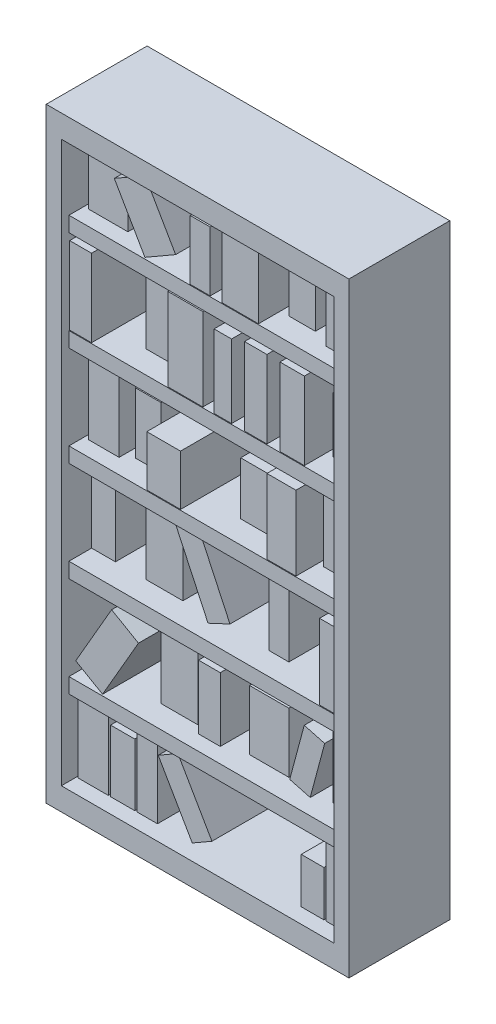
SolidWorks part; units mm, degrees
ref_plane "Front Plane" through (0, 0, 0) normal (0, 0, 1) x (1, 0, 0)
ref_plane "Top Plane" through (0, 0, 0) normal (0, 1, 0) x (1, 0, 0)
ref_plane "Right Plane" through (0, 0, 0) normal (1, 0, 0) x (0, 0, -1)
sketch "Sketch1" plane through (0, 0, 0) normal (0, 1, 0) x (1, 0, 0)
  line L1 (-50, 16.6667) -> (50, 16.6667)
  line L2 (-50, 16.6667) -> (-50, -16.6667)
  line L3 (-50, -16.6667) -> (50, -16.6667)
  line L4 (50, 16.6667) -> (50, -16.6667)
  line L5 (-50, 16.6667) -> (50, -16.6667) construction
  line L6 (-50, -16.6667) -> (50, 16.6667) construction
  point P0 (0, 0)
  dimension "D1" = 100
  dimension "D2" = 33.3333
extrude "Boss-Extrude1" add sketch "Sketch1" along normal mid plane 200
sketch "Sketch2" plane through (0, 0, 16.6667) normal (0, 0, 1) x (1, 0, 0)
  line L0 (50, 100) -> (50, -100) construction
  line L1 (-45, 92.5) -> (45, 92.5)
  line L2 (-45, 92.5) -> (-45, -92.5)
  line L3 (-45, -92.5) -> (45, -92.5)
  line L4 (45, 92.5) -> (45, -92.5)
  line L5 (-45, 92.5) -> (45, -92.5) construction
  line L6 (-45, -92.5) -> (45, 92.5) construction
  line L7 (-50, -100) -> (50, -100) construction
  point P0 (0, 0)
  dimension "D1" = 5
  dimension "D2" = 7.5
extrude "Cut-Extrude1" cut sketch "Sketch2" against normal blind 27.5
sketch "Sketch3" plane through (0, 0, -10.8333) normal (0, 0, 1) x (1, 0, 0)
  line L0 (45, -92.5) -> (45, 92.5) construction
  line L1 (45, -62.5) -> (-45, -62.5)
  line L2 (45, -62.5) -> (45, -67.5)
  line L3 (45, -67.5) -> (-45, -67.5)
  line L4 (-45, -62.5) -> (-45, -67.5)
  line L5 (-45, 92.5) -> (-45, -92.5) construction
  line L6 (-45, -92.5) -> (45, -92.5) construction
  line L7 (45, -29.5) -> (-45, -29.5)
  line L8 (45, -34.5) -> (-45, -34.5)
  line L9 (45, -29.5) -> (45, -34.5)
  line L10 (-45, -29.5) -> (-45, -34.5)
  line L11 (45, 3.5) -> (-45, 3.5)
  line L12 (45, -1.5) -> (-45, -1.5)
  line L13 (45, 3.5) -> (45, -1.5)
  line L14 (-45, 3.5) -> (-45, -1.5)
  line L15 (45, 36.5) -> (-45, 36.5)
  line L16 (45, 31.5) -> (-45, 31.5)
  line L17 (45, 36.5) -> (45, 31.5)
  line L18 (-45, 36.5) -> (-45, 31.5)
  line L19 (45, 69.5) -> (-45, 69.5)
  line L20 (45, 64.5) -> (-45, 64.5)
  line L21 (45, 69.5) -> (45, 64.5)
  line L22 (-45, 69.5) -> (-45, 64.5)
  dimension "D1" = 25
  dimension "D2" = 5
  dimension "D4" = 33
  dimension "D3" = 5
extrude "Boss-Extrude2" add sketch "Sketch3" along normal blind 25
sketch "Sketch4" plane through (0, 0, -10.8333) normal (0, 0, 1) x (1, 0, 0)
  line L0 (37.5, -92.5) -> (37.5, -70)
  line L1 (-45, -92.5) -> (45, -92.5) construction
  line L2 (37.5, -70) -> (45, -70)
  line L3 (45, -92.5) -> (45, 92.5) construction
  line L4 (45, -70) -> (45, -92.5)
  line L5 (45, -92.5) -> (37.5, -92.5)
  line L6 (36.75, -92.5) -> (36.75, -77.5)
  line L7 (-45, -92.5) -> (45, -92.5) construction
  line L8 (36.75, -77.5) -> (29.25, -77.5)
  line L9 (29.25, -77.5) -> (29.25, -92.5)
  line L10 (29.25, -92.5) -> (36.75, -92.5)
  line L11 (-44.5, -92.5) -> (-44.5, -70)
  line L12 (-44.5, -70) -> (-34.5, -70)
  line L13 (-34.5, -70) -> (-34.5, -92.5)
  line L14 (-34.5, -92.5) -> (-44.5, -92.5)
  line L15 (-45, 92.5) -> (-45, -92.5) construction
  line L16 (-33.7477, -92.5) -> (-33.7477, -72)
  line L17 (-33.7477, -72) -> (-25.7477, -72)
  line L18 (-25.7477, -72) -> (-25.7477, -92.5)
  line L19 (-25.7477, -92.5) -> (-33.7477, -92.5)
  line L20 (-24.9977, -92.5) -> (-24.9977, -70)
  line L21 (-24.9977, -70) -> (-18.2477, -70)
  line L22 (-18.2477, -70) -> (-18.2477, -92.5)
  line L23 (-18.2477, -92.5) -> (-24.9977, -92.5)
  line L24 (-17.9977, -72.7644) -> (-6.7477, -92.25)
  line L25 (-6.7477, -92.25) -> (-0.2525, -88.5)
  line L26 (-0.2525, -88.5) -> (-11.5025, -69.0144)
  line L27 (-11.5025, -69.0144) -> (-17.9977, -72.7644)
  line L28 (-17.9977, -70) -> (-17.9977, -92.5) construction
  line L29 (-18.2477, -92.25) -> (29.25, -92.25) construction
  point P25 (-29.7477, -72)
  point P34 (0, 0)
  dimension "D1" = 22.5
  dimension "D2" = 7.5
  dimension "D3" = 7.5
  dimension "D4" = 15
  dimension "D5" = 0.75
  dimension "D6" = 10
  dimension "D7" = 0.5
  dimension "D8" = 0.7523
  dimension "D9" = 2
  dimension "D10" = 8
  dimension "D11" = 0.75
  dimension "D12" = 7.5
  dimension "D13" = 30
  dimension "D14" = 7.5
  dimension "D15" = 22.5
  dimension "D16" = 0.25
  dimension "D17" = 0.25
extrude "Boss-Extrude5" add sketch "Sketch4" along normal offset from surface (22.5 mm away) 5 contours L14 L11 L12 L13 | L19 L16 L17 L18 | L23 L20 L21 L22 | L27 L24 L25 L26 | L10 L6 L8 L9 | L5 L0 L2 L4 up to face at (0, 0, 16.6667)
sketch "Sketch5" plane through (0, 0, -10.8333) normal (0, 0, 1) x (1, 0, 0)
  line L0 (45, -62.5) -> (45, -40.0606)
  line L1 (45, -92.5) -> (45, 92.5) construction
  line L2 (45, -40.0606) -> (34.7546, -40.0606)
  line L3 (34.7546, -40.0606) -> (34.7546, -62.5)
  line L4 (45, -62.5) -> (-45, -62.5) construction
  line L5 (34.7546, -62.5) -> (45, -62.5)
  line L6 (20.163, -42.7136) -> (7.1632, -42.7136)
  line L7 (7.1632, -42.7136) -> (7.1632, -62.5)
  line L8 (7.1632, -62.5) -> (20.163, -62.5)
  line L9 (45, -62.5) -> (-45, -62.5) construction
  line L10 (20.163, -62.5) -> (20.163, -42.7136)
  line L11 (-9.8162, -62.5) -> (-9.8162, -36.877)
  line L12 (-9.8162, -36.877) -> (-22.0201, -36.877)
  line L13 (-22.0201, -36.877) -> (-22.0201, -62.5)
  line L14 (-22.0201, -62.5) -> (-9.8162, -62.5)
  line L15 (-45, -6.3672) -> (-37.1423, -6.3672)
  line L16 (-45, -1.5) -> (-45, -29.5) construction
  line L17 (-37.1423, -6.3672) -> (-37.1423, -29.5)
  line L18 (45, -29.5) -> (-45, -29.5) construction
  line L19 (-37.1423, -29.5) -> (-45, -29.5)
  line L20 (-45, -29.5) -> (-45, -6.3672)
  line L21 (-27.0608, -4.5) -> (-14.8569, -4.5)
  line L22 (-14.8569, -4.5) -> (-14.8569, -29.5)
  line L23 (45, -29.5) -> (-45, -29.5) construction
  line L24 (-14.8569, -29.5) -> (-27.0608, -29.5)
  line L25 (-27.0608, -29.5) -> (-27.0608, -4.5)
  line L26 (13.5304, -29.5) -> (13.5304, -8.755)
  line L27 (13.5304, -8.755) -> (20.163, -8.755)
  line L28 (20.163, -8.755) -> (20.163, -29.5)
  line L29 (20.163, -29.5) -> (13.5304, -29.5)
  line L30 (42, 3.5) -> (42, 25.9996)
  line L31 (45, 3.5) -> (-45, 3.5) construction
  line L32 (42, 25.9996) -> (31.6532, 25.9996)
  line L33 (31.6532, 25.9996) -> (31.6532, 3.5)
  line L34 (31.6532, 3.5) -> (42, 3.5)
  line L35 (16.8467, 3.5) -> (16.8467, 20.9589)
  line L36 (45, 3.5) -> (-45, 3.5) construction
  line L37 (16.8467, 20.9589) -> (4.2448, 20.9589)
  line L38 (4.2448, 20.9589) -> (4.2448, 3.5)
  line L39 (4.2448, 3.5) -> (16.8467, 3.5)
  line L40 (-22.0201, 3.5) -> (-22.0201, 23.6119)
  line L41 (-22.0201, 23.6119) -> (-30.5097, 23.6119)
  line L42 (-30.5097, 23.6119) -> (-30.5097, 3.5)
  line L43 (-30.5097, 3.5) -> (-22.0201, 3.5)
  line L44 (45, 54.9175) -> (34.7546, 54.9175)
  line L45 (45, 36.5) -> (45, 64.5) construction
  line L46 (34.7546, 54.9175) -> (34.7546, 36.5)
  line L47 (45, 36.5) -> (-45, 36.5) construction
  line L48 (34.7546, 36.5) -> (45, 36.5)
  line L49 (45, 36.5) -> (-45, 36.5) construction
  line L50 (45, 36.5) -> (45, 54.9175)
  line L51 (-14.8569, 36.5) -> (-14.8569, 58.3664)
  line L52 (-14.8569, 58.3664) -> (-27.0608, 58.3664)
  line L53 (-27.0608, 58.3664) -> (-27.0608, 36.5)
  line L54 (-27.0608, 36.5) -> (-14.8569, 36.5)
  line L55 (20.163, 69.5) -> (20.163, 89.1415)
  line L56 (45, 69.5) -> (-45, 69.5) construction
  line L57 (20.163, 89.1415) -> (28.9179, 89.1415)
  line L58 (28.9179, 89.1415) -> (28.9179, 69.5)
  line L59 (45, 69.5) -> (-45, 69.5) construction
  line L60 (28.9179, 69.5) -> (20.163, 69.5)
  line L61 (-45, 92.5) -> (-45, -92.5) construction
  dimension "D1" = 22.4394
  dimension "D2" = 10.2454
  dimension "D3" = 12.9998
  dimension "D4" = 19.7864
  dimension "D5" = 14.5916
  dimension "D6" = 16.9793
  dimension "D7" = 25.623
  dimension "D8" = 12.2039
  dimension "D9" = 20.745
  dimension "D10" = 6.6326
  dimension "D11" = 12.2039
  dimension "D12" = 23.1328
  dimension "D13" = 7.8577
  dimension "D14" = 10.0815
  dimension "D15" = 25
  dimension "D16" = 8.4897
  dimension "D17" = 20.1119
  dimension "D18" = 12.6018
  dimension "D19" = 17.4589
  dimension "D20" = 26.2649
  dimension "D21" = 10.3468
  dimension "D22" = 22.4996
  dimension "D23" = 3
  dimension "D24" = 18.4175
  dimension "D25" = 10.2454
  dimension "D26" = 21.8664
  dimension "D27" = 17.9392
  dimension "D28" = 8.755
  dimension "D29" = 19.6415
extrude "Boss-Extrude6" add sketch "Sketch5" along normal offset from surface (17.5 mm away) 10 contours L60 L55 L57 L58 | L54 L51 L52 L53 | L50 L44 L46 L48 | L39 L35 L37 L38 | L34 L30 L32 L33 | L43 L40 L41 L42 | L25 L21 L22 L24 | L20 L15 L17 L19 | L29 L26 L27 L28 | L14 L11 L12 L13 | L10 L6 L7 L8 | L5 L0 L2 L3 up to face at (0, 0, 16.6667)
sketch "Sketch6" plane through (0, 0, -10.8333) normal (0, 0, 1) x (1, 0, 0)
  line L0 (-7.1632, -62.5) -> (-7.1632, -41.3871)
  line L1 (45, -62.5) -> (-45, -62.5) construction
  line L2 (-7.1632, -41.3871) -> (0, -41.3871)
  line L3 (0, -41.3871) -> (0, -62.5)
  line L4 (0, -62.5) -> (-7.1632, -62.5)
  line L5 (27.7431, -42.5686) -> (34.5046, -44.3804)
  line L6 (34.5046, -44.3804) -> (29.7164, -62.25)
  line L7 (29.7164, -62.25) -> (22.9549, -60.4383)
  line L8 (22.9549, -60.4383) -> (27.7431, -42.5686)
  line L9 (-14.6069, -6.5923) -> (-4.0415, -29.25)
  line L10 (-4.0415, -29.25) -> (3.209, -25.8691)
  line L11 (3.209, -25.8691) -> (-7.3565, -3.2114)
  line L12 (-7.3565, -3.2114) -> (-14.6069, -6.5923)
  line L13 (-43.5, 28.4287) -> (-33.4282, 28.4287)
  line L14 (-33.4282, 28.4287) -> (-33.4282, 3.5)
  line L15 (-30.5097, 3.5) -> (-45, 3.5) construction
  line L16 (-33.4282, 3.5) -> (-43.5, 3.5)
  line L17 (-43.5, 3.5) -> (-43.5, 28.4287)
  line L18 (34.8604, 92.5) -> (34.8604, 69.5)
  line L19 (45, 92.5) -> (-45, 92.5) construction
  line L20 (45, 69.5) -> (28.9179, 69.5) construction
  line L21 (34.8604, 69.5) -> (42.5, 69.5)
  line L22 (45, 69.5) -> (-45, 69.5) construction
  line L23 (42.5, 69.5) -> (42.5, 92.5)
  line L24 (42.5, 92.5) -> (34.8604, 92.5)
  line L25 (-43.5, 69.5) -> (-43.5, 89.2312)
  line L26 (20.163, 69.5) -> (-45, 69.5) construction
  line L27 (-43.5, 89.2312) -> (-30.5097, 89.2312)
  line L28 (-30.5097, 89.2312) -> (-30.5097, 69.5)
  line L29 (-30.5097, 69.5) -> (-43.5, 69.5)
  line L30 (34.5046, -40.0606) -> (34.5046, -62.5) construction
  line L31 (45, -40.0606) -> (34.7546, -40.0606) construction
  line L32 (34.7546, -62.5) -> (34.7546, -40.0606) construction
  line L33 (34.5046, -62.25) -> (20.163, -62.25) construction
  line L34 (20.163, -42.7136) -> (20.163, -62.5) construction
  line L35 (34.7546, -62.5) -> (20.163, -62.5) construction
  line L36 (-14.6069, -29.5) -> (-14.6069, -4.5) construction
  line L37 (13.5304, -29.5) -> (-14.8569, -29.5) construction
  line L38 (-27.0608, -4.5) -> (-14.8569, -4.5) construction
  line L39 (-14.8569, -29.5) -> (-14.8569, -4.5) construction
  line L40 (-14.8569, -29.25) -> (13.5304, -29.25) construction
  line L41 (13.5304, -8.755) -> (13.5304, -29.5) construction
  line L42 (-45, 92.5) -> (-45, -92.5) construction
  line L43 (45, 69.5) -> (45, 92.5) construction
  point P52 (0, 0)
  dimension "D1" = 7.1632
  dimension "D2" = 21.1129
  dimension "D3" = 0.25
  dimension "D4" = 0.25
  dimension "D5" = 15
  dimension "D6" = 7
  dimension "D7" = 18.5
  dimension "D8" = 0.25
  dimension "D9" = 0.25
  dimension "D10" = 25
  dimension "D11" = 8
  dimension "D12" = 25
  dimension "D13" = 24.9287
  dimension "D14" = 1.5
  dimension "D15" = 10.0718
  dimension "D16" = 12.9903
  dimension "D17" = 19.7312
  dimension "D18" = 7.6396
  dimension "D19" = 2.5
extrude "Boss-Extrude7" add sketch "Sketch6" along normal offset from surface (20 mm away) 7.5 up to face at (0, 0, 16.6667)
sketch "Sketch7" plane through (0, 0, -10.8333) normal (0, 0, 1) x (1, 0, 0)
  line L0 (-22.2701, -41.7032) -> (-31.1443, -36.5797)
  line L1 (-31.1443, -36.5797) -> (-43.007, -57.1265)
  line L2 (-43.007, -57.1265) -> (-34.1328, -62.25)
  line L3 (-34.1328, -62.25) -> (-22.2701, -41.7032)
  line L4 (37.5569, -29.5) -> (37.5569, -4.6754)
  line L5 (45, -29.5) -> (-45, -29.5) construction
  line L6 (37.5569, -4.6754) -> (45, -4.6754)
  line L7 (45, -29.5) -> (45, -1.5) construction
  line L8 (45, -4.6754) -> (45, -29.5)
  line L9 (45, -29.5) -> (20.163, -29.5) construction
  line L10 (45, -29.5) -> (37.5569, -29.5)
  line L11 (-19.5201, 3.5) -> (-19.5201, 20.1913)
  line L12 (4.2448, 3.5) -> (-22.0201, 3.5) construction
  line L13 (-19.5201, 20.1913) -> (-8.3782, 20.1913)
  line L14 (-8.3782, 20.1913) -> (-8.3782, 3.5)
  line L15 (-8.3782, 3.5) -> (-19.5201, 3.5)
  line L16 (29.7606, 28.0763) -> (29.7606, 3.5)
  line L17 (31.6532, 3.5) -> (16.8467, 3.5) construction
  line L18 (29.7606, 3.5) -> (20.163, 3.5)
  line L19 (20.163, 3.5) -> (20.163, 28.0763)
  line L20 (20.163, 28.0763) -> (29.7606, 28.0763)
  line L21 (-45, 62.1169) -> (-37.7779, 62.1169)
  line L22 (-45, 64.5) -> (-45, 36.5) construction
  line L23 (-37.7779, 62.1169) -> (-37.7779, 36.5)
  line L24 (-27.0608, 36.5) -> (-45, 36.5) construction
  line L25 (-37.7779, 36.5) -> (-45, 36.5)
  line L26 (-45, 36.5) -> (-45, 62.1169)
  line L27 (-12.5725, 36.5) -> (-12.5725, 63.8038)
  line L28 (34.7546, 36.5) -> (-14.8569, 36.5) construction
  line L29 (-12.5725, 63.8038) -> (-1.0052, 63.8038)
  line L30 (-1.0052, 63.8038) -> (-1.0052, 36.5)
  line L31 (-1.0052, 36.5) -> (-12.5725, 36.5)
  line L32 (2.7125, 36.5) -> (2.7125, 60.6988)
  line L33 (45, 36.5) -> (-45, 36.5) construction
  line L34 (2.7125, 60.6988) -> (8.4868, 60.6988)
  line L35 (8.4868, 60.6988) -> (8.4868, 36.5)
  line L36 (8.4868, 36.5) -> (2.7125, 36.5)
  line L37 (12.7582, 62.1169) -> (20.163, 62.1169)
  line L38 (20.163, 62.1169) -> (20.163, 36.5)
  line L39 (20.163, 36.5) -> (12.7582, 36.5)
  line L40 (12.7582, 36.5) -> (12.7582, 62.1169)
  line L41 (24.4649, 62.1169) -> (24.4649, 36.5)
  line L42 (24.4649, 36.5) -> (32.533, 36.5)
  line L43 (32.533, 36.5) -> (32.533, 62.1169)
  line L44 (32.533, 62.1169) -> (24.4649, 62.1169)
  line L45 (-30.2597, 87.2849) -> (-20.1359, 69.75)
  line L46 (45, 69.5) -> (-45, 69.5) construction
  line L47 (-20.1359, 69.75) -> (-9.9949, 75.605)
  line L48 (-9.9949, 75.605) -> (-20.1187, 93.1399)
  line L49 (-20.1187, 93.1399) -> (-30.2597, 87.2849)
  line L50 (17.3755, 69.5) -> (17.3755, 91.527)
  line L51 (20.163, 69.5) -> (-30.5097, 69.5) construction
  line L52 (17.3755, 91.527) -> (5.3398, 91.527)
  line L53 (5.3398, 91.527) -> (5.3398, 69.5)
  line L54 (5.3398, 69.5) -> (17.3755, 69.5)
  line L55 (1.4321, 69.5) -> (1.4321, 89.2129)
  line L56 (1.4321, 89.2129) -> (-5.1734, 89.2129)
  line L57 (-5.1734, 89.2129) -> (-5.1734, 69.5)
  line L58 (-5.1734, 69.5) -> (1.4321, 69.5)
  line L59 (-22.2701, -62.5) -> (-22.2701, -36.877) construction
  line L60 (-22.0201, -62.5) -> (-45, -62.5) construction
  line L61 (-9.8162, -36.877) -> (-22.0201, -36.877) construction
  line L62 (-22.0201, -62.5) -> (-22.0201, -36.877) construction
  line L63 (-22.0201, -62.25) -> (-45, -62.25) construction
  line L64 (-45, 92.5) -> (-45, -92.5) construction
  line L65 (45, -62.5) -> (-45, -62.5) construction
  line L66 (31.6532, 3.5) -> (31.6532, 25.9996) construction
  line L67 (-22.0201, 3.5) -> (-22.0201, 23.6119) construction
  line L68 (34.7546, 54.9175) -> (34.7546, 36.5) construction
  line L69 (20.163, 69.5) -> (20.163, 89.1415) construction
  line L70 (-30.2597, 69.5) -> (-30.2597, 89.2312) construction
  line L71 (-30.5097, 89.2312) -> (-43.5, 89.2312) construction
  line L72 (-30.5097, 89.2312) -> (-30.5097, 69.5) construction
  line L73 (-30.2597, 69.75) -> (-5.1734, 69.75) construction
  point P85 (0, 0)
  point P100 (0, 0)
  dimension "D1" = 0.25
  dimension "D2" = 0.25
  dimension "D3" = 10.247
  dimension "D4" = 23.7254
  dimension "D5" = 30
  dimension "D6" = 7.4431
  dimension "D7" = 24.8246
  dimension "D8" = 9.5976
  dimension "D9" = 1.8926
  dimension "D10" = 24.5763
  dimension "D11" = 16.6913
  dimension "D12" = 11.1419
  dimension "D13" = 2.5
  dimension "D14" = 7.2221
  dimension "D15" = 25.6169
  dimension "D16" = 8.0682
  dimension "D17" = 25.6169
  dimension "D18" = 2.2215
  dimension "D19" = 7.4048
  dimension "D20" = 4.2714
  dimension "D21" = 24.1988
  dimension "D22" = 5.7743
  dimension "D23" = 3.7177
  dimension "D24" = 27.3038
  dimension "D25" = 11.5673
  dimension "D26" = 2.7874
  dimension "D27" = 22.027
  dimension "D28" = 12.0357
  dimension "D29" = 3.9077
  dimension "D30" = 19.7129
  dimension "D31" = 0.25
  dimension "D32" = 0.25
  dimension "D33" = 30
  dimension "D34" = 11.7099
  dimension "D35" = 20.2476
extrude "Boss-Extrude9" add sketch "Sketch7" along normal offset from surface (24.75 mm away) 2.75 up to face at (0, 0, 16.6667)
